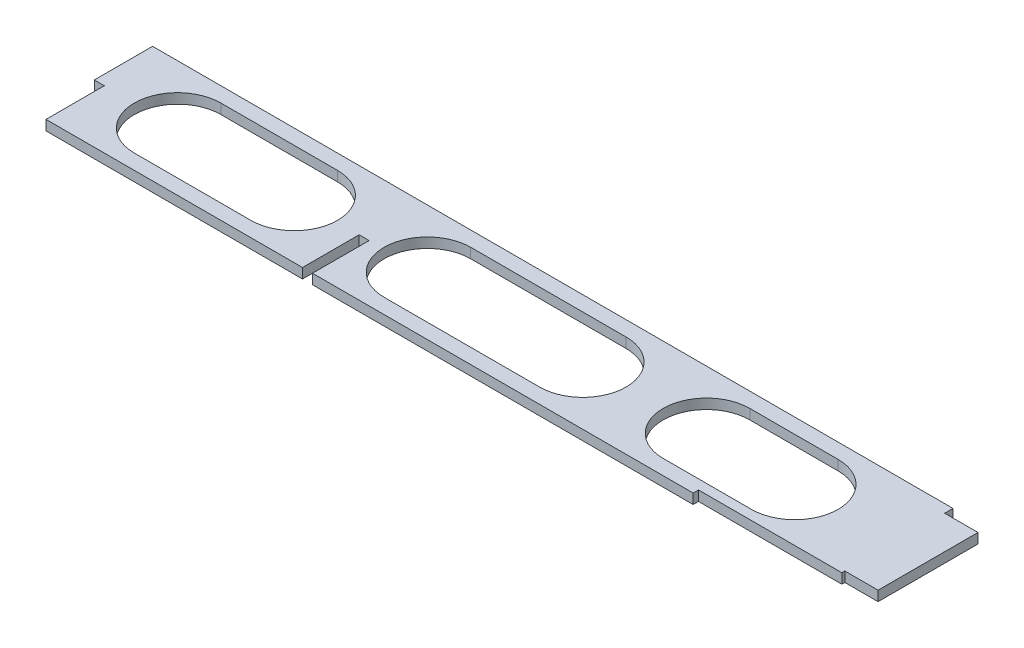
SolidWorks part; units mm, degrees
material "Pine"
ref_plane "Front Plane" through (0, 0, 0) normal (0, 0, 1) x (1, 0, 0)
ref_plane "Top Plane" through (0, 0, 0) normal (0, 1, 0) x (1, 0, 0)
ref_plane "Right Plane" through (0, 0, 0) normal (1, 0, 0) x (0, 0, -1)
sketch "Sketch1" plane through (0, 0, 0) normal (0, 1, 0) x (1, 0, 0)
  line L1 (0, 17.5) -> (250.28, 17.5)
  line L2 (0, 17.5) -> (0, -17.5)
  line L3 (0, -17.5) -> (250.28, -17.5)
  line L4 (250.28, 17.5) -> (250.28, -17.5)
  point P4 (0, 0)
  dimension "D1" = 35
  dimension "D2" = 250.28
extrude "Boss-Extrude1" add sketch "Sketch1" along normal blind 3
sketch "Sketch2" plane through (0, 3, 0) normal (0, 1, 0) x (1, 0, 0)
  line L0 (0, -17.5) -> (250.28, -17.5) construction
  line L1 (80, -17.5) -> (83, -17.5)
  line L2 (80, -17.5) -> (80, -0.5)
  line L3 (80, -0.5) -> (83, -0.5)
  line L4 (83, -17.5) -> (83, -0.5)
  line L5 (0, 17.5) -> (0, -17.5) construction
  line L27 (250.28, -17.5) -> (250.28, 17.5) construction
  line L28 (250.28, -7.5) -> (250.28, 7.5) construction
  point P14 (81.5, -0.5)
  point P21 (250.28, 0)
  dimension "D1" = 17
  dimension "D2" = 3
  dimension "D3" = 80
  dimension "D6" = 15
  dimension "D4" = 168.78
extrude "Cut-Extrude1" cut sketch "Sketch2" against normal through all both
sketch "Sketch4" plane through (0, 3, 0) normal (0, 1, 0) x (1, 0, 0)
  line L0 (0, 0) -> (25, 0) construction
  line L1 (250.28, 17.5) -> (250.28, -17.5) construction
  line L2 (146.6552, 13) -> (146.6552, -13) construction
  line L3 (183.7624, 13) -> (183.7624, -13) construction
  line L6 (146.6552, 13) -> (183.7624, 13) construction
  line L7 (183.7624, 13) -> (210.28, 13)
  line L8 (25, 0) -> (60, 0) construction
  line L9 (25, 13) -> (60, 13)
  line L10 (25, -13) -> (60, -13)
  line L11 (146.6552, -13) -> (183.7624, -13) construction
  line L12 (183.7624, -13) -> (210.28, -13)
  line L19 (100, 0) -> (210.28, 0) construction
  line L20 (100, 13) -> (146.6552, 13)
  line L21 (100, -13) -> (146.6552, -13)
  arc A2 (25, 13) -> (25, -13) centre (25, 0) ccw
  arc A3 (60, -13) -> (60, 13) centre (60, 0) ccw
  arc A4 (100, 13) -> (100, -13) centre (100, 0) ccw
  arc A5 (210.28, -13) -> (210.28, 13) centre (210.28, 0) ccw
  arc A6 (146.6552, 13) -> (146.6552, -13) centre (146.6552, 0) cw
  arc A7 (183.7624, -13) -> (183.7624, 13) centre (183.7624, 0) cw
  point P6 (42.5, 0)
  point P28 (162.64, 0)
  dimension "D1" = 25
  dimension "D2" = 13
  dimension "D3" = 40
  dimension "D4" = 60
  dimension "D5" = 100
extrude "Cut-Extrude3" cut sketch "Sketch4" against normal through all
sketch "Sketch5" plane through (0, 3, 0) normal (0, 1, 0) x (1, 0, 0)
  line L0 (240.28, 17.5) -> (240.28, 15)
  line L1 (0, 17.5) -> (250.28, 17.5) construction
  line L2 (240.28, 15) -> (250.28, 15)
  line L3 (250.28, 17.5) -> (250.28, -17.5) construction
  line L4 (250.28, 15) -> (250.28, 17.5)
  line L5 (250.28, 17.5) -> (240.28, 17.5)
  line L7 (250.28, -17.5) -> (240.28, -17.5)
  line L8 (250.28, -17.5) -> (250.28, -15)
  line L9 (250.28, -15) -> (240.28, -15)
  line L10 (240.28, -17.5) -> (240.28, -15)
  dimension "D1" = 30
  dimension "D2" = 10
extrude "Cut-Extrude4" cut sketch "Sketch5" against normal up to surface (3 mm away) up to face at (197.0212, 0, 0)
sketch "Sketch6" plane through (0, 3, 0) normal (0, 1, 0) x (1, 0, 0)
  line L0 (0, -17.5) -> (250.28, -17.5) construction
  line L1 (0, 0) -> (3, 0)
  line L2 (0, 0) -> (0, -17.5)
  line L3 (0, -17.5) -> (3, -17.5)
  line L4 (3, 0) -> (3, -17.5)
  dimension "D1" = 3
extrude "Cut-Extrude5" cut sketch "Sketch6" against normal blind 10
sketch "Sketch7" plane through (0, 0, 17.5) normal (0, 0, 1) x (1, 0, 0)
  line L0 (0, 0) -> (250.28, 0) construction
  line L1 (240.28, 3) -> (197.28, 3)
  line L2 (240.28, 3) -> (240.28, 0)
  line L3 (240.28, 0) -> (197.28, 0)
  line L4 (197.28, 3) -> (197.28, 0)
  dimension "D1" = 43
extrude "Cut-Extrude6" cut sketch "Sketch7" against normal blind 1.6
